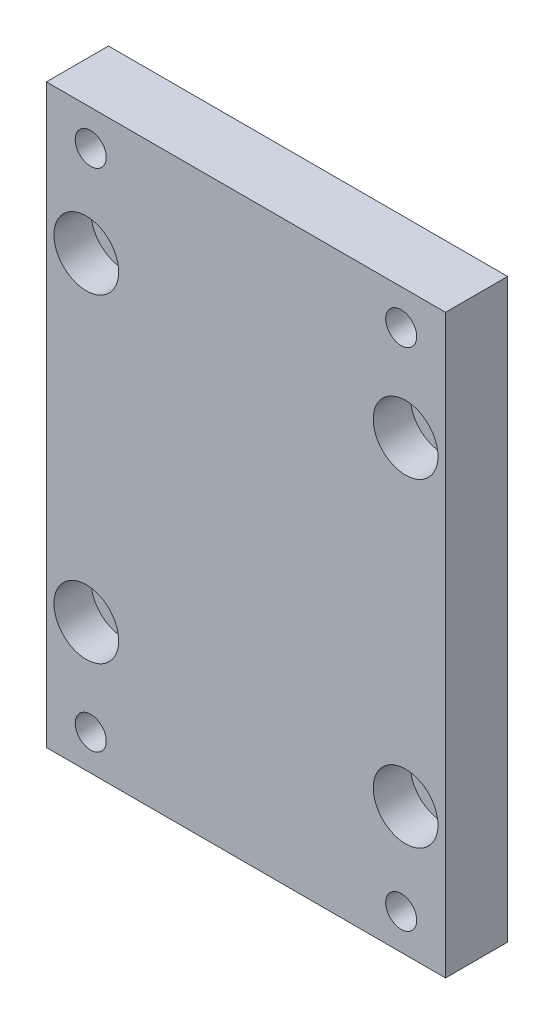
SolidWorks part; units mm, degrees
ref_plane "前基準面" through (0, 0, 0) normal (0, 0, 1) x (1, 0, 0)
ref_plane "上基準面" through (0, 0, 0) normal (0, 1, 0) x (1, 0, 0)
ref_plane "右基準面" through (0, 0, 0) normal (1, 0, 0) x (0, 0, -1)
sketch "草圖2" plane through (0, 0, 0) normal (0, 0, 1) x (1, 0, 0)
  line L0 (0, 0) -> (0, 30.0174) construction
  line L1 (-22.5, 32.5) -> (22.5, 32.5)
  line L2 (-22.5, 32.5) -> (-22.5, -32.5)
  line L3 (-22.5, -32.5) -> (22.5, -32.5)
  line L4 (22.5, 32.5) -> (22.5, -32.5)
  line L5 (-22.5, 32.5) -> (22.5, -32.5) construction
  line L6 (-22.5, -32.5) -> (22.5, 32.5) construction
  line L7 (0, -55) -> (0, 55) construction
  line L8 (0, 0) -> (-44.8344, 0) construction
  line L9 (55, 0) -> (-55, 0) construction
  line L10 (57, 0) -> (12.1656, 0) construction
  line L11 (57, -36) -> (12.1656, -36) construction
  line L12 (0, -36) -> (-44.8344, -36) construction
  circle A0 centre (-18, 18) radius 2.25
  circle A1 centre (-17.5, 28.5) radius 1.75
  circle A2 centre (18, 18) radius 2.25
  circle A3 centre (18, -18) radius 2.25
  circle A4 centre (-18, -18) radius 2.25
  circle A8 centre (17.5, 28.5) radius 1.75
  circle A9 centre (17.5, -28.5) radius 1.75
  circle A10 centre (-17.5, -28.5) radius 1.75
  point P0 (0, 0)
  dimension "D3" = 4.5
  dimension "D6" = 3.5
  dimension "D9" = 17.5
  dimension "D10" = 28.5
  dimension "D1" = 45
  dimension "D2" = 65
  dimension "D4" = 36
  dimension "D5" = 36
extrude "填料-伸長1" add sketch "草圖2" along normal blind 7
hole_wizard "鑽孔1" positions "3D草圖1" profile "草圖3" legacy end condition through all
sketch3d "3D草圖1"
  line L0 (-18, 18, 7) -> (-18, 18, 0) construction
  line L1 (18, 18, 7) -> (18, 18, 0) construction
  line L2 (18, -18, 7) -> (18, -18, 0) construction
  line L3 (-18, -18, 7) -> (-18, -18, 0) construction
  point P0 (-18, 18, 7)
  point P4 (18, 18, 7)
  point P8 (18, -18, 7)
  point P12 (-18, -18, 7)
sketch "草圖3" plane through (-18, 18, 7) normal (1, 0, 0) x (0, -1, 0)
  line L0 (0, 0) -> (0, 7)
  line L1 (0, 7) -> (2.25, 7)
  line L2 (2.25, 7) -> (2.25, 4.2)
  line L3 (2.25, 4.2) -> (3.65, 4.2)
  line L4 (3.65, 4.2) -> (3.65, 0)
  line L5 (3.65, 0) -> (0, 0)
  line L6 (0, 110) -> (0, -10) construction
  dimension "直徑" = 4.5
  dimension "深度" = 7
  dimension "柱孔直徑1" = 7.3
  dimension "柱孔深度1" = 4.2
sketch "草圖4" plane through (0, 0, 0) normal (0, 0, -1) x (-1, 0, 0)
  line L0 (0, 55) -> (0, -55) construction
  line L1 (-14.2091, 28.5) -> (-15.8546, 31.35)
  line L2 (-15.8546, 31.35) -> (-19.1454, 31.35)
  line L3 (-19.1454, 31.35) -> (-20.7909, 28.5)
  line L4 (-20.7909, 28.5) -> (-19.1454, 25.65)
  line L5 (-19.1454, 25.65) -> (-15.8546, 25.65)
  line L6 (-15.8546, 25.65) -> (-14.2091, 28.5)
  line L25 (15.8546, 25.65) -> (14.2091, 28.5)
  line L26 (19.1454, 25.65) -> (15.8546, 25.65)
  line L27 (20.7909, 28.5) -> (19.1454, 25.65)
  line L28 (19.1454, 31.35) -> (20.7909, 28.5)
  line L29 (15.8546, 31.35) -> (19.1454, 31.35)
  line L30 (14.2091, 28.5) -> (15.8546, 31.35)
  line L31 (55, 0) -> (-55, 0) construction
  line L32 (14.2091, -28.5) -> (15.8546, -31.35)
  line L33 (15.8546, -31.35) -> (19.1454, -31.35)
  line L34 (19.1454, -31.35) -> (20.7909, -28.5)
  line L35 (20.7909, -28.5) -> (19.1454, -25.65)
  line L36 (19.1454, -25.65) -> (15.8546, -25.65)
  line L37 (15.8546, -25.65) -> (14.2091, -28.5)
  line L38 (-15.8546, -25.65) -> (-14.2091, -28.5)
  line L39 (-19.1454, -25.65) -> (-15.8546, -25.65)
  line L40 (-20.7909, -28.5) -> (-19.1454, -25.65)
  line L41 (-19.1454, -31.35) -> (-20.7909, -28.5)
  line L42 (-15.8546, -31.35) -> (-19.1454, -31.35)
  line L43 (-14.2091, -28.5) -> (-15.8546, -31.35)
  circle A0 centre (-17.5, 28.5) radius 2.85 construction
  circle A1 centre (17.5, 28.5) radius 2.85 construction
  circle A2 centre (17.5, -28.5) radius 2.85 construction
  circle A3 centre (-17.5, -28.5) radius 2.85 construction
  dimension "D1" = 5.7
extrude "除料-伸長1" cut sketch "草圖4" against normal blind 2.5
